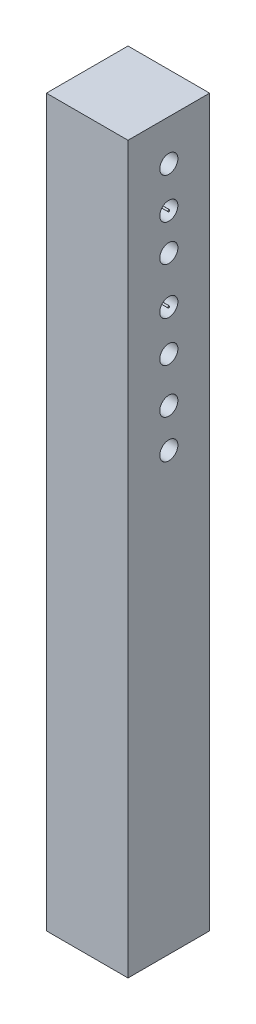
SolidWorks part; units mm, degrees
ref_plane "Front Plane" through (0, 0, 0) normal (0, 0, 1) x (1, 0, 0)
ref_plane "Top Plane" through (0, 0, 0) normal (0, 1, 0) x (1, 0, 0)
ref_plane "Right Plane" through (0, 0, 0) normal (1, 0, 0) x (0, 0, -1)
sketch "Sketch1" plane through (0, 0, 0) normal (0, 1, 0) x (1, 0, 0)
  line L1 (-88.5189, -53.6417) -> (1.4811, -53.6417)
  line L2 (-88.5189, -53.6417) -> (-88.5189, 36.3583)
  line L3 (-88.5189, 36.3583) -> (1.4811, 36.3583)
  line L4 (1.4811, -53.6417) -> (1.4811, 36.3583)
extrude "Boss-Extrude1" add sketch "Sketch1" against normal blind 800
sketch "Sketch2" plane through (1.4811, 0, 0) normal (1, 0, 0) x (0, 0, -1)
  circle A0 centre (-8.6417, -44.9675) radius 10
  circle A1 centre (-8.6417, -89.8203) radius 1
  circle A2 centre (-8.6417, -130.1879) radius 10
  circle A3 centre (-8.6417, -181.7687) radius 1
  circle A4 centre (-8.6417, -226.6215) radius 10
  circle A5 centre (-8.6417, -275.9597) radius 10
  circle A6 centre (-8.6417, -318.5699) radius 10
  circle A7 centre (-8.6417, -181.7687) radius 10
  circle A8 centre (-8.6417, -89.8203) radius 10
extrude "Cut-Extrude1" cut sketch "Sketch2" against normal through all
